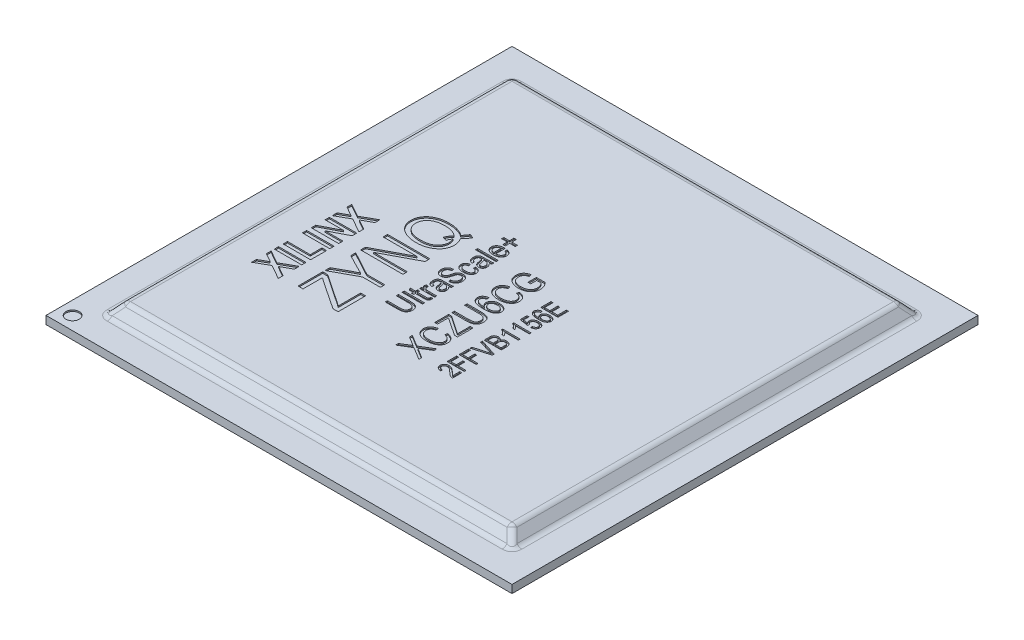
SolidWorks part; units mm, degrees
ref_plane "Front Plane" through (0, 0, 0) normal (0, 0, 1) x (1, 0, 0)
ref_plane "Top Plane" through (0, 0, 0) normal (0, 1, 0) x (1, 0, 0)
ref_plane "Right Plane" through (0, 0, 0) normal (1, 0, 0) x (0, 0, -1)
sketch "Sketch1" plane through (0, 0, 0) normal (0, 1, 0) x (1, 0, 0)
  line L1 (-17.5, 17.5) -> (17.5, 17.5)
  line L2 (-17.5, 17.5) -> (-17.5, -17.5)
  line L3 (-17.5, -17.5) -> (17.5, -17.5)
  line L4 (17.5, 17.5) -> (17.5, -17.5)
  line L5 (-17.5, 17.5) -> (17.5, -17.5) construction
  line L6 (-17.5, -17.5) -> (17.5, 17.5) construction
  point P0 (0, 0)
  dimension "D1" = 35
extrude "Boss-Extrude1" add sketch "Sketch1" along normal blind 1.5
sketch "Sketch2" plane through (0, 0, 17.5) normal (0, 0, 1) x (1, 0, 0)
  line L0 (-17.5, 0.6) -> (-15.35, 0.6)
  line L1 (-17.5, 1.5) -> (-17.5, 0) construction
  line L2 (-15.35, 0.6) -> (-14.55, 1.5)
  line L3 (-17.5, 1.5) -> (17.5, 1.5) construction
  line L4 (-14.55, 1.5) -> (-17.5, 1.5)
  line L5 (-17.5, 1.5) -> (-17.5, 0.6)
  line L6 (17.5, 0.6) -> (15.35, 0.6)
  line L7 (17.5, 1.5) -> (17.5, 0) construction
  line L8 (15.35, 0.6) -> (14.55, 1.5)
  line L9 (14.55, 1.5) -> (17.5, 1.5)
  line L10 (17.5, 1.5) -> (17.5, 0.6)
  dimension "D1" = 14.55
  dimension "D2" = 15.35
  dimension "D3" = 0.9
extrude "Cut-Extrude1" cut sketch "Sketch2" against normal through all
sketch "Sketch3" plane through (17.5, 0, 0) normal (1, 0, 0) x (0, 0, -1)
  line L0 (-17.5, 0.6) -> (-15.35, 0.6)
  line L1 (17.5, 0.6) -> (-17.5, 0.6) construction
  line L2 (-15.35, 0.6) -> (-14.55, 1.5)
  line L3 (17.5, 1.5) -> (-17.5, 1.5) construction
  line L4 (-14.55, 1.5) -> (-17.5, 1.5)
  line L5 (-17.5, 1.5) -> (-17.5, 0.6)
  line L6 (17.5, 0.6) -> (17.5, 1.5)
  line L7 (17.5, 1.5) -> (14.55, 1.5)
  line L8 (14.55, 1.5) -> (15.35, 0.6)
  line L9 (17.5, 0.6) -> (-17.5, 0.6) construction
  line L10 (15.35, 0.6) -> (17.5, 0.6)
  dimension "D1" = 14.55
  dimension "D2" = 15.35
extrude "Cut-Extrude2" cut sketch "Sketch3" against normal through all
fillet "Fillet1" radius 0.5 12 edges at (14.95, 1.05, 14.95) (15.35, 0.6, 0) (14.55, 1.5, 0) (14.95, 1.05, -14.95) (0, 1.5, -14.55) (0, 0.6, -15.35) (-14.95, 1.05, -14.95) (-15.35, 0.6, 0) (0, 0.6, 15.35) (0, 1.5, 14.55) (-14.55, 1.5, 0) (-14.95, 1.05, 14.95)
sketch "Sketch4" plane through (0, 0.6, 0) normal (0, 1, 0) x (1, 0, 0)
  line L0 (-17.5, -17.5) -> (17.5, -17.5) construction
  line L1 (-17.5, 17.5) -> (-17.5, -17.5) construction
  circle A0 centre (-16.5, -16.5) radius 0.5
  dimension "D1" = 1
  dimension "D2" = 1
  dimension "D3" = 1
extrude "Cut-Extrude3" cut sketch "Sketch4" against normal blind 0.1
sketch "Sketch5" plane through (0, 1.5, 0) normal (0, 1, 0) x (1, 0, 0)
  line L0 (-79.584, 20.8588) -> (-79.584, 140.6193) construction
sketch "Sketch6" plane through (0, 1.5, 0) normal (0, 1, 0) x (1, 0, 0)
  line L0 (-10.2804, -7.2736) -> (-10.2804, 1.8343) construction
  line L1 (-5.8673, -7.2736) -> (-5.8673, 4.1348) construction
  line L2 (-3.1913, -4.9262) -> (-3.1913, 5.4493) construction
  line L3 (0.2565, -7.2736) -> (0.2565, 5.1852) construction
  line L4 (2.7473, -7.2736) -> (2.7473, 5.1852) construction
  text T0 "<b>XILINX</b>" font "Arial Narrow" height in points 8
  text T1 "ZYNQ" font "Arial Narrow" height 3.175
  text T2 "UltraScale+" font "Arial Narrow" height in points 6
  text T3 "XCZU6CG" font "Arial Narrow" height in points 7
  text T4 "2FFVB1156E\r\n" font "Arial Narrow" height in points 5
extrude "Cut-Extrude4" cut sketch "Sketch6" against normal blind 0.1
